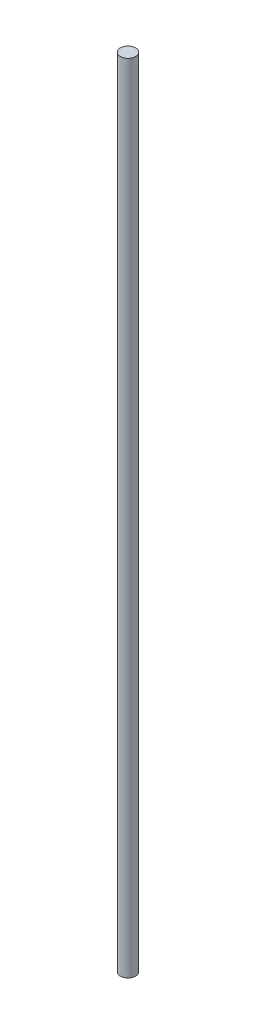
SolidWorks part; units mm, degrees
ref_plane "Front Plane" through (0, 0, 0) normal (0, 0, 1) x (1, 0, 0)
ref_plane "Top Plane" through (0, 0, 0) normal (0, 1, 0) x (1, 0, 0)
ref_plane "Right Plane" through (0, 0, 0) normal (1, 0, 0) x (0, 0, -1)
sketch "Sketch1" plane through (0, 0, 0) normal (0, 1, 0) x (1, 0, 0)
  circle A0 centre (0, 0) radius 4
  dimension "D1" = 8
extrude "Boss-Extrude1" add sketch "Sketch1" along normal blind 420
ref_point "Point1"
